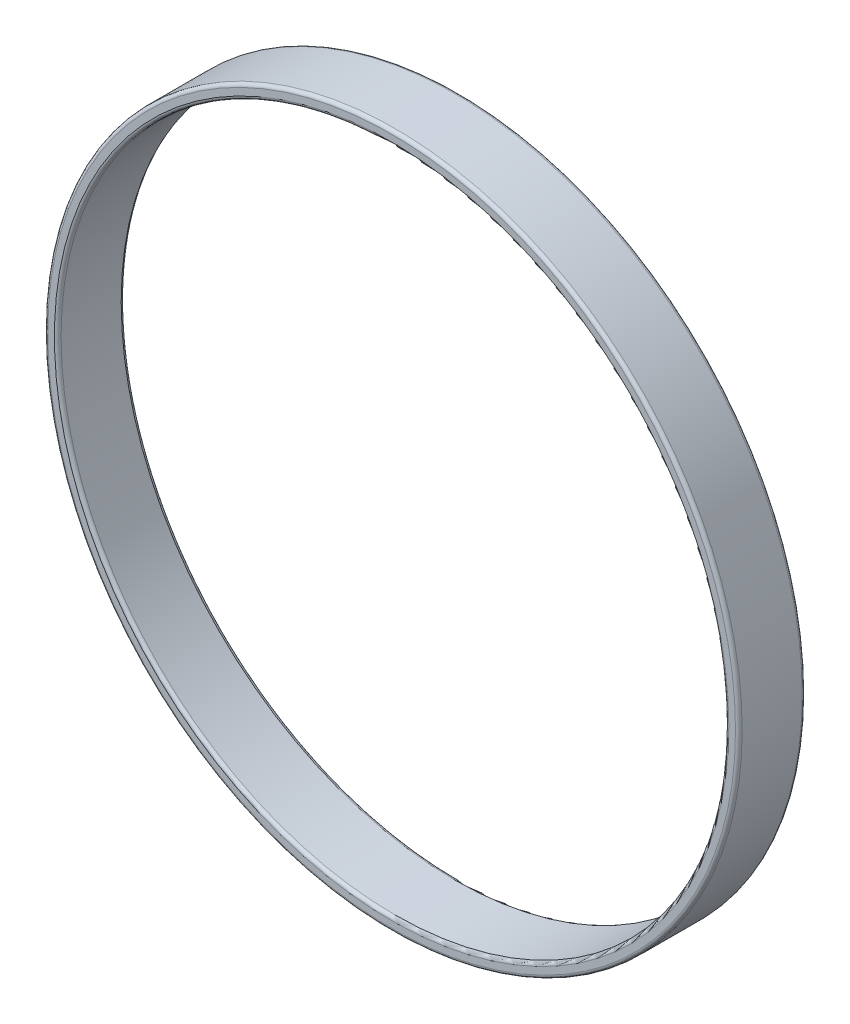
SolidWorks part; units mm, degrees
ref_plane "Front Plane" through (0, 0, 0) normal (0, 0, 1) x (1, 0, 0)
ref_plane "Top Plane" through (0, 0, 0) normal (0, 1, 0) x (1, 0, 0)
ref_plane "Right Plane" through (0, 0, 0) normal (1, 0, 0) x (0, 0, -1)
sketch "Sketch1" plane through (0, 0, 0) normal (0, 0, 1) x (1, 0, 0)
  circle A0 centre (0, 0) radius 50
  circle A1 centre (0, 0) radius 52
  dimension "D1" = 100
  dimension "D2" = 2
extrude "Boss-Extrude1" add sketch "Sketch1" along normal blind 10
fillet "Fillet1" radius 0.5 4 edges at (50, 0, 10) (52, 0, 10) (50, 0, 0) (52, 0, 0)
